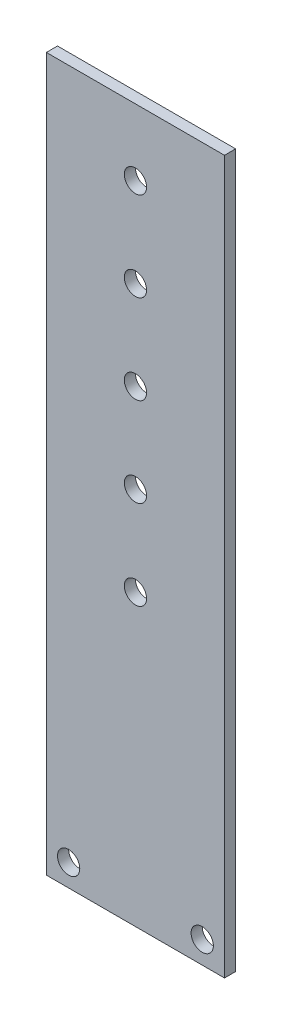
SolidWorks part; units mm, degrees
material "AISI 1020"
ref_plane "Front Plane" through (0, 0, 0) normal (0, 0, 1) x (1, 0, 0)
ref_plane "Top Plane" through (0, 0, 0) normal (0, 1, 0) x (1, 0, 0)
ref_plane "Right Plane" through (0, 0, 0) normal (1, 0, 0) x (0, 0, -1)
sketch "Sketch1" plane through (0, 0, 0) normal (0, 0, 1) x (1, 0, 0)
  line L0 (25.4, 0) -> (25.4, 203.2) construction
  line L1 (0, 0) -> (50.8, 0)
  line L2 (0, 0) -> (0, 203.2)
  line L3 (0, 203.2) -> (50.8, 203.2)
  line L4 (50.8, 0) -> (50.8, 203.2)
  circle A0 centre (6.35, 6.35) radius 3.175
  circle A1 centre (44.45, 6.35) radius 3.175
  circle A2 centre (25.4, 184.2) radius 3.175
  circle A3 centre (25.4, 158.8) radius 3.175
  circle A4 centre (25.4, 133.4) radius 3.175
  circle A5 centre (25.4, 108) radius 3.175
  circle A6 centre (25.4, 82.6) radius 3.175
  point P21 (0, 0)
  point P23 (27.5827, 118.4391)
  dimension "D1" = 6.35
  dimension "D2" = 6.35
  dimension "D7" = 6.35
  dimension "D8" = 19
  dimension "D10" = 6.35
  dimension "D11" = 6.35
  dimension "D12" = 6.35
  dimension "D13" = 6.35
  dimension "D3" = 38.1
  dimension "D4" = 6.35
  dimension "D5" = 50.8
  dimension "D6" = 203.2
  dimension "D9" = 6.35
  dimension "D14" = 25.4
  dimension "D15" = 25.4
  dimension "D16" = 25.4
  dimension "D17" = 25.4
extrude "Boss-Extrude1" add sketch "Sketch1" along normal blind 3.175
